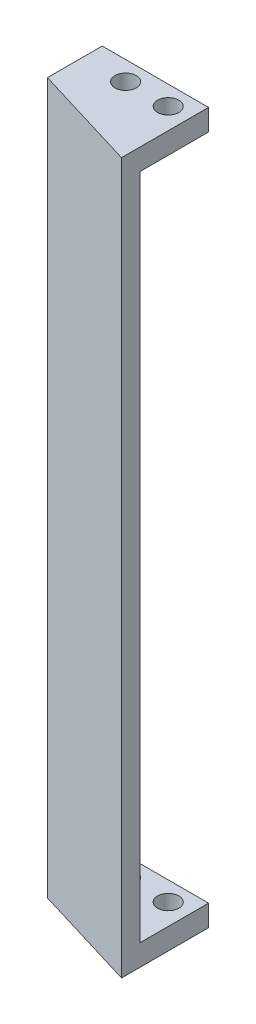
SolidWorks part; units mm, degrees
ref_plane "Front Plane" through (0, 0, 0) normal (0, 0, 1) x (1, 0, 0)
ref_plane "Top Plane" through (0, 0, 0) normal (0, 1, 0) x (1, 0, 0)
ref_plane "Right Plane" through (0, 0, 0) normal (1, 0, 0) x (0, 0, -1)
sketch "Sketch1" plane through (0, 0, 0) normal (0, 1, 0) x (1, 0, 0)
  line L0 (-51.6187, -8.7512) -> (-51.6187, 3.5026)
  line L1 (-51.6187, 3.5026) -> (-66.588, 3.5026)
  line L2 (-66.588, 3.5026) -> (-66.588, -4.2063)
  line L3 (-66.588, -4.2063) -> (-51.6187, -8.7512)
  circle A0 centre (-54.588, 0.7937) radius 1.5
  circle A1 centre (-60.588, 0.7937) radius 1.5
extrude "Boss-Extrude1" add sketch "Sketch1" along normal blind 3
sketch "Sketch2" plane through (0, 3, 0) normal (0, 1, 0) x (1, 0, 0)
  line L0 (-66.588, 3.5026) -> (-66.588, -4.2063)
  line L1 (-66.588, -4.2063) -> (-51.6187, -8.7512)
  line L2 (-64.088, 3.5026) -> (-66.588, 3.5026)
  line L3 (-66.588, -4.2063) -> (-51.6187, -8.7512)
  line L4 (-64.088, -2.3526) -> (-64.088, 3.5026)
  line L6 (-64.088, 3.5026) -> (-64.088, -2.3526)
  line L7 (-63.3612, -5.186) -> (-61.9328, -5.6196)
  line L8 (-51.6187, -6.1385) -> (-51.6187, -8.7512)
  line L9 (-61.9207, -3.0106) -> (-64.088, -2.3526)
  line L10 (-64.088, -2.3526) -> (-51.6187, -6.1385)
  line L11 (-51.6187, -8.7512) -> (-51.6187, 3.5026) construction
  line M2 (-66.588, -4.2063) -> (-51.6187, -8.7512)
  line M3 (-51.6187, -8.7512) -> (-51.6187, 3.5026)
  line M4 (-51.6187, 3.5026) -> (-66.588, 3.5026)
  line M5 (-66.588, 3.5026) -> (-66.588, -4.2063)
extrude "Boss-Extrude2" add sketch "Sketch2" along normal blind 94 contours L10 L9 L4 L3 M4 M5 M2 M3
sketch "Sketch3" plane through (-6.0632, 0, 19.9699) normal (0.2905, 0, -0.9569) x (-0.9569, 0, -0.2905)
  line L0 (47.6089, 3) -> (47.6089, 50)
  line L1 (47.6089, 97) -> (47.6089, 3) construction
  line L2 (47.6089, 50) -> (60.6402, 50)
  line L3 (60.6402, 97) -> (60.6402, 3) construction
ref_plane "Plane1" through (0, 50, 0) normal (0, -1, 0) x (-1, 0, 0)
mirror "Mirror1" about plane through (0, 50, 0) normal (0, -1, 0) of "Boss-Extrude1"
